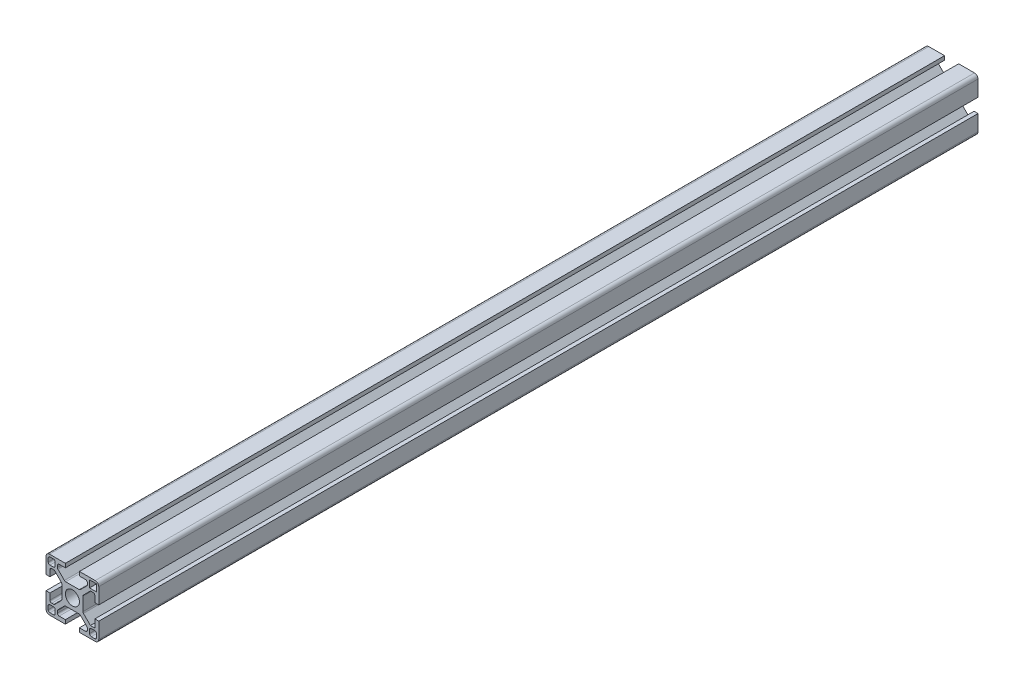
SolidWorks part; units mm, degrees
ref_plane "Front Plane" through (0, 0, 0) normal (0, 0, 1) x (1, 0, 0)
ref_plane "Top Plane" through (0, 0, 0) normal (0, 1, 0) x (1, 0, 0)
ref_plane "Right Plane" through (0, 0, 0) normal (1, 0, 0) x (0, 0, -1)
sketch "Sketch1" plane through (0, 0, 0) normal (0, 0, 1) x (1, 0, 0)
  line B0 (9.75, -10.75) -> (9.75, -12.75)
  arc B1 (9.75, -12.75) -> (10.75, -13.75) centre (10.75, -12.75) ccw
  line B2 (10.75, -13.75) -> (12.75, -13.75)
  arc B3 (12.75, -13.75) -> (13.75, -12.75) centre (12.75, -12.75) ccw
  line B4 (13.75, -12.75) -> (13.75, -10.75)
  arc B5 (13.75, -10.75) -> (12.75, -9.75) centre (12.75, -10.75) ccw
  line B6 (12.75, -9.75) -> (10.75, -9.75)
  arc B7 (10.75, -9.75) -> (9.75, -10.75) centre (10.75, -10.75) ccw
  circle B8 centre (0, 0) radius 4
  line B9 (13.75, 9.75) -> (13.75, 13.75)
  line B10 (13.75, 13.75) -> (9.75, 13.75)
  line B11 (9.75, 13.75) -> (9.75, 9.75)
  line B12 (9.75, 9.75) -> (13.75, 9.75)
  line B13 (-15, -4) -> (-15, -13)
  arc B14 (-15, -13) -> (-13, -15) centre (-13, -13) ccw
  line B15 (-13, -15) -> (-4, -15)
  line B16 (-4, -15) -> (-4, -12.75)
  line B17 (-4, -12.75) -> (-7.5, -12.75)
  arc B18 (-8.5, -11.75) -> (-7.5, -12.75) centre (-7.5, -11.75) ccw
  line B19 (-8.5, -11.75) -> (-8.5, -10.682)
  arc B20 (-8.2071, -9.9749) -> (-8.5, -10.682) centre (-7.5, -10.682) ccw
  line B21 (-8.2071, -9.9749) -> (-4.5251, -6.2929)
  arc B22 (-3.818, -6) -> (-4.5251, -6.2929) centre (-3.818, -7) ccw
  line B23 (-3.818, -6) -> (3.818, -6)
  arc B24 (4.5251, -6.2929) -> (3.818, -6) centre (3.818, -7) ccw
  line B25 (4.5251, -6.2929) -> (8.2071, -9.9749)
  arc B26 (8.5, -10.682) -> (8.2071, -9.9749) centre (7.5, -10.682) ccw
  line B27 (8.5, -10.682) -> (8.5, -11.75)
  arc B28 (7.5, -12.75) -> (8.5, -11.75) centre (7.5, -11.75) ccw
  line B29 (7.5, -12.75) -> (4, -12.75)
  line B30 (4, -12.75) -> (4, -15)
  line B31 (4, -15) -> (13, -15)
  arc B32 (13, -15) -> (15, -13) centre (13, -13) ccw
  line B33 (15, -13) -> (15, -4)
  line B34 (15, -4) -> (12.75, -4)
  line B35 (12.75, -4) -> (12.75, -8.5)
  line B36 (12.75, -8.5) -> (10.2678, -8.5)
  line B37 (10.2678, -8.5) -> (6.2929, -4.5251)
  arc B38 (6, -3.818) -> (6.2929, -4.5251) centre (7, -3.818) ccw
  line B39 (6, -3.818) -> (6, 3.818)
  arc B40 (6.2929, 4.5251) -> (6, 3.818) centre (7, 3.818) ccw
  line B41 (6.2929, 4.5251) -> (9.9749, 8.2071)
  arc B42 (10.682, 8.5) -> (9.9749, 8.2071) centre (10.682, 7.5) ccw
  line B43 (10.682, 8.5) -> (11.75, 8.5)
  arc B44 (12.75, 7.5) -> (11.75, 8.5) centre (11.75, 7.5) ccw
  line B45 (12.75, 7.5) -> (12.75, 4)
  line B46 (12.75, 4) -> (15, 4)
  line B47 (15, 4) -> (15, 13)
  arc B48 (15, 13) -> (13, 15) centre (13, 13) ccw
  line B49 (13, 15) -> (4, 15)
  line B50 (4, 15) -> (4, 12.75)
  line B51 (4, 12.75) -> (7.5, 12.75)
  arc B52 (8.5, 11.75) -> (7.5, 12.75) centre (7.5, 11.75) ccw
  line B53 (8.5, 11.75) -> (8.5, 10.682)
  arc B54 (8.2071, 9.9749) -> (8.5, 10.682) centre (7.5, 10.682) ccw
  line B55 (8.2071, 9.9749) -> (4.5251, 6.2929)
  arc B56 (3.818, 6) -> (4.5251, 6.2929) centre (3.818, 7) ccw
  line B57 (3.818, 6) -> (-3.818, 6)
  arc B58 (-4.5251, 6.2929) -> (-3.818, 6) centre (-3.818, 7) ccw
  line B59 (-4.5251, 6.2929) -> (-8.2071, 9.9749)
  arc B60 (-8.5, 10.682) -> (-8.2071, 9.9749) centre (-7.5, 10.682) ccw
  line B61 (-8.5, 10.682) -> (-8.5, 11.75)
  arc B62 (-7.5, 12.75) -> (-8.5, 11.75) centre (-7.5, 11.75) ccw
  line B63 (-7.5, 12.75) -> (-4, 12.75)
  line B64 (-4, 12.75) -> (-4, 15)
  line B65 (-4, 15) -> (-13, 15)
  arc B66 (-13, 15) -> (-15, 13) centre (-13, 13) ccw
  line B67 (-15, 13) -> (-15, 4)
  line B68 (-15, 4) -> (-12.75, 4)
  line B69 (-12.75, 4) -> (-12.75, 7.5)
  arc B70 (-11.75, 8.5) -> (-12.75, 7.5) centre (-11.75, 7.5) ccw
  line B71 (-11.75, 8.5) -> (-10.682, 8.5)
  arc B72 (-9.9749, 8.2071) -> (-10.682, 8.5) centre (-10.682, 7.5) ccw
  line B73 (-9.9749, 8.2071) -> (-6.2929, 4.5251)
  arc B74 (-6, 3.818) -> (-6.2929, 4.5251) centre (-7, 3.818) ccw
  line B75 (-6, 3.818) -> (-6, -3.818)
  arc B76 (-6.2929, -4.5251) -> (-6, -3.818) centre (-7, -3.818) ccw
  line B77 (-6.2929, -4.5251) -> (-9.9749, -8.2071)
  arc B78 (-10.682, -8.5) -> (-9.9749, -8.2071) centre (-10.682, -7.5) ccw
  line B79 (-10.682, -8.5) -> (-11.75, -8.5)
  arc B80 (-12.75, -7.5) -> (-11.75, -8.5) centre (-11.75, -7.5) ccw
  line B81 (-12.75, -7.5) -> (-12.75, -4)
  line B82 (-12.75, -4) -> (-15, -4)
  line B83 (-10.75, 13.75) -> (-12.75, 13.75)
  arc B84 (-12.75, 13.75) -> (-13.75, 12.75) centre (-12.75, 12.75) ccw
  line B85 (-13.75, 12.75) -> (-13.75, 10.75)
  arc B86 (-13.75, 10.75) -> (-12.75, 9.75) centre (-12.75, 10.75) ccw
  line B87 (-12.75, 9.75) -> (-10.75, 9.75)
  arc B88 (-10.75, 9.75) -> (-9.75, 10.75) centre (-10.75, 10.75) ccw
  line B89 (-9.75, 10.75) -> (-9.75, 12.75)
  arc B90 (-9.75, 12.75) -> (-10.75, 13.75) centre (-10.75, 12.75) ccw
  line B91 (-12.75, -13.75) -> (-10.75, -13.75)
  arc B92 (-10.75, -13.75) -> (-9.75, -12.75) centre (-10.75, -12.75) ccw
  line B93 (-9.75, -12.75) -> (-9.75, -10.75)
  arc B94 (-9.75, -10.75) -> (-10.75, -9.75) centre (-10.75, -10.75) ccw
  line B95 (-10.75, -9.75) -> (-12.75, -9.75)
  arc B96 (-12.75, -9.75) -> (-13.75, -10.75) centre (-12.75, -10.75) ccw
  line B97 (-13.75, -10.75) -> (-13.75, -12.75)
  arc B98 (-13.75, -12.75) -> (-12.75, -13.75) centre (-12.75, -12.75) ccw
sketch_block_instance "3030-1"
sketch_block "3030"
extrude "Boss-Extrude1" add sketch "Sketch1" along normal blind 500
